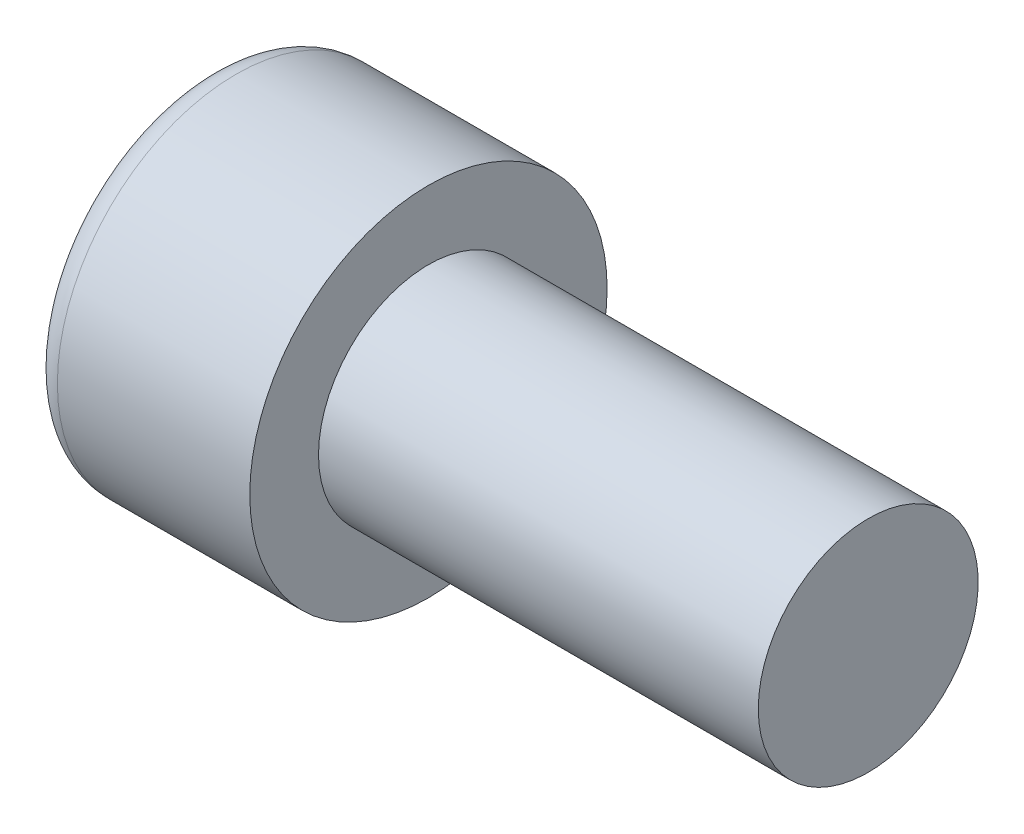
SolidWorks part; units mm, degrees
material "AISI 1020"
ref_plane "Спереди" through (0, 0, 0) normal (0, 0, 1) x (1, 0, 0)
ref_plane "Сверху" through (0, 0, 0) normal (0, 1, 0) x (1, 0, 0)
ref_plane "Справа" through (0, 0, 0) normal (1, 0, 0) x (0, 0, -1)
sketch "Эскиз1" plane through (0, 0, 0) normal (0, 0, 1) x (1, 0, 0)
  line L0 (-351.5896, 0) -> (17227.8895, 0) construction
  line L1 (-8, 0) -> (-8, 6.5)
  line L2 (-8, 6.5) -> (0, 6.5)
  line L3 (0, 6.5) -> (0, 4)
  line L4 (0, 4) -> (16, 4)
  line L5 (16, 4) -> (16, 0)
  line L6 (-8, 0) -> (16, 0)
  dimension "D1" = 8
  dimension "D2" = 16
  dimension "D3" = 13
  dimension "D4" = 8
revolve "Повернуть1" add sketch "Эскиз1" angle 360 about L0
cosmetic thread "Условное изображение резьбы1" parameters "D2"=6.619
sketch "Эскиз2" plane through (-8, 0, 0) normal (-1, 0, 0) x (0, 0, 1)
  line L1 (0, -3.4641) -> (3, -1.7321)
  line L2 (3, -1.7321) -> (3, 1.7321)
  line L3 (3, 1.7321) -> (0, 3.4641)
  line L4 (0, 3.4641) -> (-3, 1.7321)
  line L5 (-3, 1.7321) -> (-3, -1.7321)
  line L6 (-3, -1.7321) -> (0, -3.4641)
  circle A0 centre (0, 0) radius 3 construction
  dimension "D1" = 6
extrude "Вырез-Вытянуть1" cut sketch "Эскиз2" against normal blind 4
fillet "Скругление1" radius 1 1 edges at (-8, 0, 6.5)
fillet "Скругление2" radius 0.2 6 edges at (-8, -2.5981, -1.5) (-8, -2.5981, 1.5) (-8, 0, 3) (-8, 2.5981, 1.5) (-8, 2.5981, -1.5) (-8, 0, -3)
